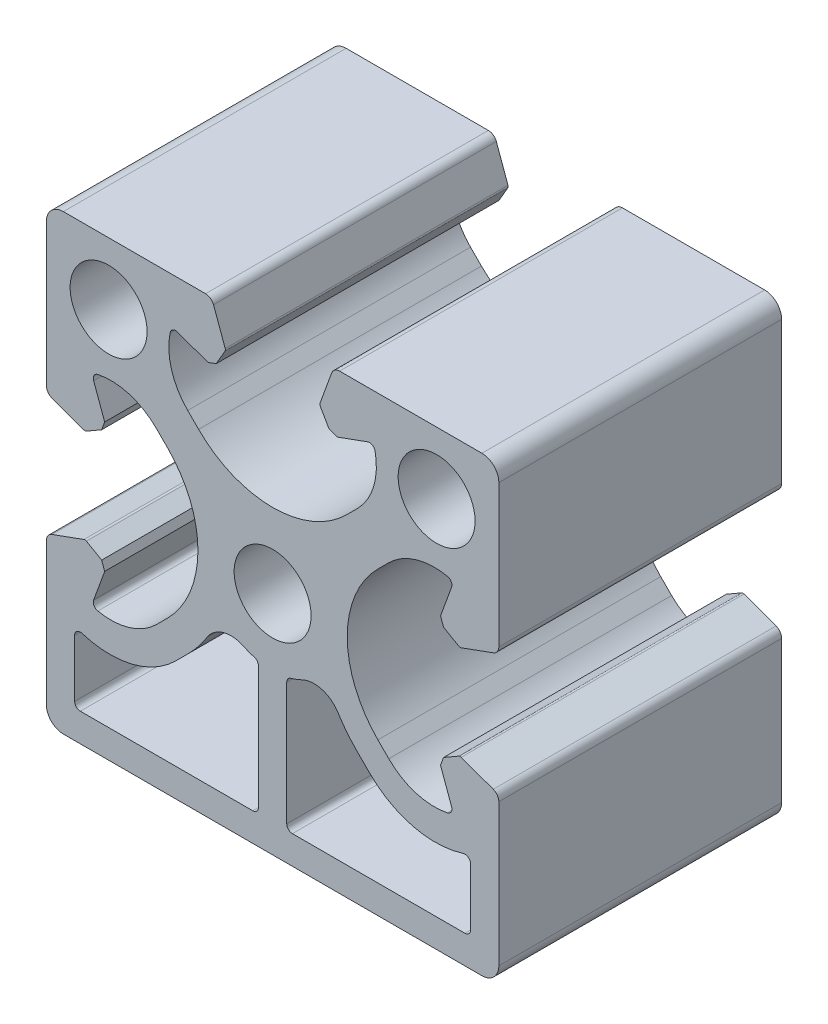
SolidWorks part; units mm, degrees
material "6005-T5"
ref_plane "Front" through (0, 0, 0) normal (0, 0, 1) x (1, 0, 0)
ref_plane "Top" through (0, 0, 0) normal (0, 1, 0) x (1, 0, 0)
ref_plane "Right" through (0, 0, 0) normal (1, 0, 0) x (0, 0, -1)
sketch "Sk Main Extrusion" plane through (0, 0, 0) normal (0, 0, 1) x (1, 0, 0)
  line L45 (-7.4415, -8.3085) -> (-8.5773, -9.4443)
  line L46 (-17.5, -11.9407) -> (-17.5, -17)
  line L47 (-17, -17.5) -> (-1.75, -17.5)
  line L48 (-1.25, -17) -> (-1.25, -6.1561)
  line L49 (1.25, -6.1561) -> (1.25, -17)
  line L50 (1.75, -17.5) -> (17, -17.5)
  line L51 (17.5, -17) -> (17.5, -11.9407)
  line L52 (8.5773, -9.4443) -> (7.4415, -8.3085)
  line L53 (-16.6712, -4.1901) -> (-19.5065, -5.2221)
  line L54 (-20, -5.9268) -> (-20, -18.5)
  line L55 (-18.5, -20) -> (18.5, -20)
  line L56 (20, -18.5) -> (20, -5.9268)
  line L57 (19.5065, -5.2221) -> (16.6712, -4.1901)
  line L58 (16.4607, -4.2085) -> (15.1113, -4.9876)
  line L59 (15.1113, -4.9876) -> (14.8453, -5.7185)
  line L60 (14.8453, -5.7185) -> (15.8198, -8.3962)
  line L61 (10.2727, -7.5042) -> (9.3093, -6.5407)
  line L62 (9.3093, 6.5407) -> (10.2727, 7.5042)
  line L63 (15.8198, 8.3962) -> (14.8453, 5.7185)
  line L64 (14.8453, 5.7185) -> (15.1113, 4.9876)
  line L65 (15.1113, 4.9876) -> (16.4607, 4.2085)
  line L66 (16.6712, 4.1901) -> (19.5065, 5.2221)
  line L67 (20, 5.9268) -> (20, 18.5)
  line L68 (18.5, 20) -> (5.9268, 20)
  line L69 (5.2221, 19.5065) -> (4.1901, 16.6712)
  line L70 (4.2085, 16.4607) -> (4.9876, 15.1113)
  line L71 (4.9876, 15.1113) -> (5.7185, 14.8453)
  line L72 (5.7185, 14.8453) -> (8.3962, 15.8198)
  line L73 (7.5042, 10.2727) -> (6.5407, 9.3093)
  line L74 (-6.5407, 9.3093) -> (-7.5042, 10.2727)
  line L75 (-8.3962, 15.8198) -> (-5.7185, 14.8453)
  line L76 (-5.7185, 14.8453) -> (-4.9876, 15.1113)
  line L77 (-4.9876, 15.1113) -> (-4.2085, 16.4607)
  line L78 (-4.1901, 16.6712) -> (-5.2221, 19.5065)
  line L79 (-5.9268, 20) -> (-18.5, 20)
  line L80 (-20, 18.5) -> (-20, 5.9268)
  line L81 (-19.5065, 5.2221) -> (-16.6712, 4.1901)
  line L82 (-16.4607, 4.2085) -> (-15.1113, 4.9876)
  line L83 (-15.1113, 4.9876) -> (-14.8453, 5.7185)
  line L84 (-14.8453, 5.7185) -> (-15.8198, 8.3962)
  line L85 (-10.2727, 7.5042) -> (-9.3093, 6.5407)
  line L86 (-9.3093, -6.5407) -> (-10.2727, -7.5042)
  line L87 (-15.8198, -8.3962) -> (-14.8453, -5.7185)
  line L88 (-14.8453, -5.7185) -> (-15.1113, -4.9876)
  line L89 (-15.1113, -4.9876) -> (-16.4607, -4.2085)
  circle A50 centre (14.5, 14.5) radius 3.4
  circle A51 centre (0, 0) radius 3.4
  circle A52 centre (-14.5, 14.5) radius 3.4
  arc A53 (-16.8492, -11.464) -> (-8.5773, -9.4443) centre (-14.3755, -3.646) ccw
  arc A54 (-16.8492, -11.464) -> (-17.5, -11.9407) centre (-17, -11.9407) ccw
  arc A55 (-17.5, -17) -> (-17, -17.5) centre (-17, -17) ccw
  arc A56 (-1.75, -17.5) -> (-1.25, -17) centre (-1.75, -17) ccw
  arc A57 (-1.25, -6.1561) -> (-1.6133, -5.6751) centre (-1.75, -6.1561) ccw
  arc A58 (-2.5767, -5.3076) -> (-1.6133, -5.6751) centre (0, 0) ccw
  arc A59 (-2.5767, -5.3076) -> (-5.7881, -6.2308) centre (-3.6686, -7.5566) ccw
  arc A60 (-7.4415, -8.3085) -> (-5.7881, -6.2308) centre (-15.75, 0) ccw
  arc A61 (1.6133, -5.6751) -> (2.5767, -5.3076) centre (0, 0) ccw
  arc A62 (-19.5065, -5.2221) -> (-20, -5.9268) centre (-19.25, -5.9268) ccw
  arc A63 (-20, -18.5) -> (-18.5, -20) centre (-18.5, -18.5) ccw
  arc A64 (18.5, -20) -> (20, -18.5) centre (18.5, -18.5) ccw
  arc A65 (20, -5.9268) -> (19.5065, -5.2221) centre (19.25, -5.9268) ccw
  arc A66 (16.6712, -4.1901) -> (16.4607, -4.2085) centre (16.5857, -4.425) ccw
  arc A67 (15.4507, -9.057) -> (15.8198, -8.3962) centre (15.35, -8.5672) ccw
  arc A68 (10.2727, -7.5042) -> (15.4507, -9.057) centre (14.3032, -3.4737) ccw
  arc A69 (9.3093, 6.5407) -> (9.3093, -6.5407) centre (15.85, 0) ccw
  arc A70 (15.4507, 9.057) -> (10.2727, 7.5042) centre (14.3032, 3.4737) ccw
  arc A71 (15.8198, 8.3962) -> (15.4507, 9.057) centre (15.35, 8.5672) ccw
  arc A72 (16.4607, 4.2085) -> (16.6712, 4.1901) centre (16.5857, 4.425) ccw
  arc A73 (19.5065, 5.2221) -> (20, 5.9268) centre (19.25, 5.9268) ccw
  arc A74 (20, 18.5) -> (18.5, 20) centre (18.5, 18.5) ccw
  arc A75 (5.9268, 20) -> (5.2221, 19.5065) centre (5.9268, 19.25) ccw
  arc A76 (4.1901, 16.6712) -> (4.2085, 16.4607) centre (4.425, 16.5857) ccw
  arc A77 (9.057, 15.4507) -> (8.3962, 15.8198) centre (8.5672, 15.35) ccw
  arc A78 (7.5042, 10.2727) -> (9.057, 15.4507) centre (3.4737, 14.3032) ccw
  arc A79 (-6.5407, 9.3093) -> (6.5407, 9.3093) centre (0, 15.85) ccw
  arc A80 (-9.057, 15.4507) -> (-7.5042, 10.2727) centre (-3.4737, 14.3032) ccw
  arc A81 (-8.3962, 15.8198) -> (-9.057, 15.4507) centre (-8.5672, 15.35) ccw
  arc A82 (-4.2085, 16.4607) -> (-4.1901, 16.6712) centre (-4.425, 16.5857) ccw
  arc A83 (-5.2221, 19.5065) -> (-5.9268, 20) centre (-5.9268, 19.25) ccw
  arc A84 (-18.5, 20) -> (-20, 18.5) centre (-18.5, 18.5) ccw
  arc A85 (-20, 5.9268) -> (-19.5065, 5.2221) centre (-19.25, 5.9268) ccw
  arc A86 (-16.6712, 4.1901) -> (-16.4607, 4.2085) centre (-16.5857, 4.425) ccw
  arc A87 (-15.4507, 9.057) -> (-15.8198, 8.3962) centre (-15.35, 8.5672) ccw
  arc A88 (-10.2727, 7.5042) -> (-15.4507, 9.057) centre (-14.3032, 3.4737) ccw
  arc A89 (-9.3093, -6.5407) -> (-9.3093, 6.5407) centre (-15.85, 0) ccw
  arc A90 (-15.4507, -9.057) -> (-10.2727, -7.5042) centre (-14.3032, -3.4737) ccw
  arc A91 (-15.8198, -8.3962) -> (-15.4507, -9.057) centre (-15.35, -8.5672) ccw
  arc A92 (-16.4607, -4.2085) -> (-16.6712, -4.1901) centre (-16.5857, -4.425) ccw
  arc A93 (1.6133, -5.6751) -> (1.25, -6.1561) centre (1.75, -6.1561) ccw
  arc A94 (1.25, -17) -> (1.75, -17.5) centre (1.75, -17) ccw
  arc A95 (17, -17.5) -> (17.5, -17) centre (17, -17) ccw
  arc A96 (17.5, -11.9407) -> (16.8492, -11.464) centre (17, -11.9407) ccw
  arc A97 (8.5773, -9.4443) -> (16.8492, -11.464) centre (14.3755, -3.646) ccw
  arc A98 (5.7881, -6.2308) -> (7.4415, -8.3085) centre (15.75, 0) ccw
  arc A99 (5.7881, -6.2308) -> (2.5767, -5.3076) centre (3.6686, -7.5566) ccw
  point P96 (0, 0)
extrude "Main Extrusion" add sketch "Sk Main Extrusion" against normal blind 25
sketch "Threaded Insert Mate Sketch" plane through (0, 0, 0) normal (0, 0, 1) x (1, 0, 0)
  circle A0 centre (0, 12.7) radius 5.6515
  circle A1 centre (12.7, 0) radius 5.6515
  circle A2 centre (0, -12.7) radius 5.6515
  circle A3 centre (-12.7, 0) radius 5.6515
  point P2 (0, 0)
  point P4 (0, 0)
  point P5 (0, 0)
  point P12 (0, 0)
  point P13 (0, 0)
  point P14 (0, 0)
  point P15 (0, 0)
  dimension "D2" = 11.303
  dimension "D1" = 12.7
  dimension "D4" = 12.7
  dimension "D3" = 4
equation "\"Weight kg\"= round ( \"SW-Mass\" , 2 )"
equation "\"Weight lbs\"= round ( \"SW-Mass\" * 2.2046 , 2 )"
equation "\"Length mm\"= round ( \"Length@Main Extrusion\" , 2 )"
equation "\"Length in\"= round ( \"Length@Main Extrusion\" / 25.4 , 3 )"
